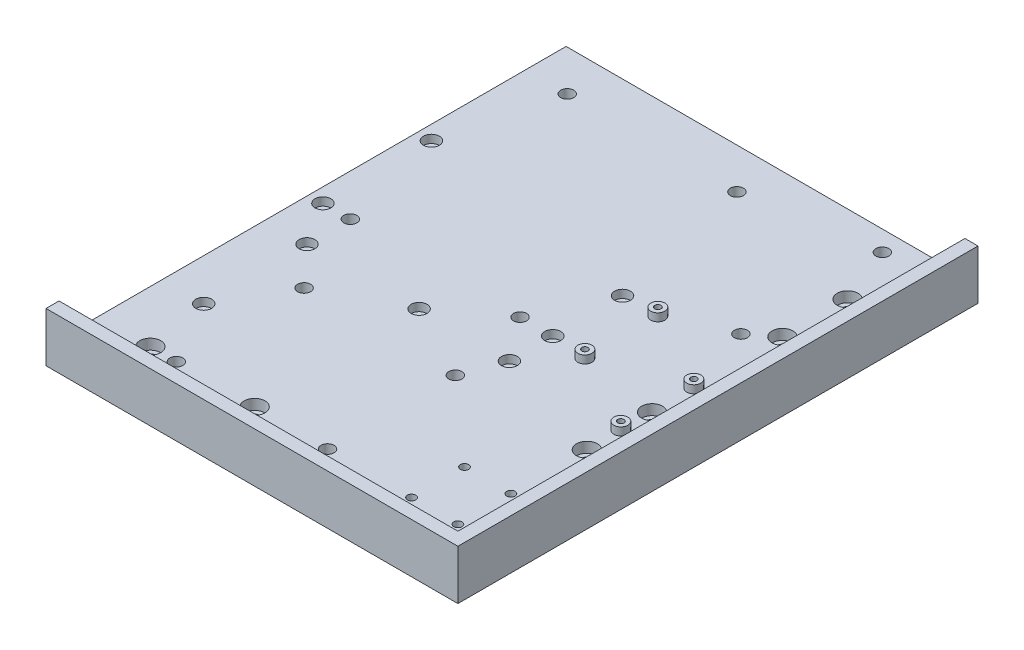
SolidWorks part; units mm, degrees
ref_plane "Front Plane" through (0, 0, 0) normal (0, 0, 1) x (1, 0, 0)
ref_plane "Top Plane" through (0, 0, 0) normal (0, 1, 0) x (1, 0, 0)
ref_plane "Right Plane" through (0, 0, 0) normal (1, 0, 0) x (0, 0, -1)
sketch "Sketch1" plane through (0, 0, 0) normal (0, 1, 0) x (1, 0, 0)
  line L1 (0, 0) -> (158, 0)
  line L2 (0, 0) -> (0, -199.5)
  line L3 (0, -199.5) -> (158, -199.5)
  line L4 (158, 0) -> (158, -199.5)
  dimension "D1" = 158
  dimension "D2" = 199.5
extrude "Boss-Extrude1" add sketch "Sketch1" along normal blind 6.35
sketch "Sketch2" [suppressed] plane through (0, 6.35, 0) normal (0, 1, 0) x (1, 0, 0)
  line L0 (0, -199.5) -> (158, -199.5) construction
  line L1 (158, -199.5) -> (77, -199.5)
  line L2 (158, -199.5) -> (158, -158.5)
  line L3 (158, -158.5) -> (77, -158.5)
  line L4 (77, -199.5) -> (77, -158.5)
  dimension "D1" = 81
  dimension "D2" = 41
sketch "Sketch3" plane through (0, 6.35, 0) normal (0, 1, 0) x (1, 0, 0)
  line L16 (158, -199.5) -> (158, 0) construction
  line L20 (0, -199.5) -> (158, -199.5) construction
  line L21 (158, -199.5) -> (158, 0)
  line L22 (0, -199.5) -> (158, -199.5)
  line L23 (0, -194.5) -> (153, -194.5)
  line L24 (153, -194.5) -> (153, 0)
  line L25 (158, 0) -> (153, 0)
  line L26 (0, -199.5) -> (0, -194.5)
  dimension "D1" = 5
extrude "Boss-Extrude2" add sketch "Sketch3" along normal blind 12.7
sketch "Sketch4" plane through (0, 6.35, 0) normal (0, -1, 0) x (1, 0, 0)
  line L0 (0, 179.5) -> (80, 179.5) construction
  line L1 (0, 0) -> (0, 199.5) construction
  line L3 (0, 199.5) -> (158, 199.5) construction
  line L4 (40, 179.5) -> (40, 188.5903) construction
  line L5 (138, 160) -> (138, 0) construction
  line L7 (158, 0) -> (0, 0) construction
  line L8 (158, 199.5) -> (158, 0) construction
  line L9 (138, 80) -> (152.6176, 80) construction
  point P8 (20, 179.5)
  point P11 (60, 179.5)
  point P20 (138, 130)
  point P21 (138, 105)
  point P22 (138, 30)
  point P23 (138, 80)
  point P24 (138, 55)
  dimension "D1" = 20
  dimension "D2" = 40
  dimension "D3" = 20
  dimension "D4" = 25
  dimension "D5" = 25
  dimension "D6" = 80
  dimension "D7" = 160
hole_wizard "CBORE for M4 SHCS1" positions "Sketch4" profile "Sketch5" counterbore size "M4" standard "ANSI Metric" end condition up to next
sketch "Sketch5" plane through (138, 6.35, 55) normal (1, 0, 0) x (0, 0, 1)
  line L0 (0, 0) -> (0, 6.35)
  line L1 (0, 6.35) -> (2.25, 6.35)
  line L3 (2.25, 6.35) -> (2.25, 4)
  line L4 (2.25, 4) -> (4, 4)
  line L5 (4, 4) -> (4, 0)
  line L7 (4, 0) -> (0, 0)
  line L11 (0, -6.35) -> (0, 107.95) construction
  dimension "Thru Hole Dia." = 4.5
  dimension "Thru Hole Depth" = 6.35
  dimension "C'Bore Dia." = 8
  dimension "C'Bore Depth" = 4
sketch "Sketch7" [suppressed] plane through (0, 0, 0) normal (0, 0, -1) x (-1, 0, 0)
  line L0 (-79, 19.05) -> (-79, 4.7647) construction
  line L1 (-158, 19.05) -> (0, 19.05) construction
  line L2 (-158, 19.05) -> (-158, 0) construction
  line L3 (-129, 19.05) -> (0, 19.05)
  line L4 (-129, 19.05) -> (-129, 9.05)
  line L5 (-129, 9.05) -> (0, 9.05)
  line L6 (0, 19.05) -> (0, 9.05)
  line L7 (0, 19.05) -> (0, 0) construction
  dimension "D2" = 10
  dimension "D3" = 29
extrude "Cut-Extrude2" [suppressed] cut sketch "Sketch7" against normal up to next
fillet "Fillet1" [suppressed] radius 5
fillet "Fillet2" [suppressed] radius 5
fillet "Fillet3" [suppressed] radius 5
sketch "Sketch8" plane through (0, 6.35, 0) normal (0, 1, 0) x (1, 0, 0)
  line L2 (153, 0) -> (153, -194.5) construction
  line L3 (153, 0) -> (0, 0) construction
  circle A0 centre (129.05, -62) radius 2.5
  circle A1 centre (129.05, -7.75) radius 2.5
  dimension "D1" = 5
  dimension "D2" = 54.25
  dimension "D3" = 23.95
  dimension "D4" = 7.75
extrude "eStop" cut sketch "Sketch8" against normal through all
sketch "Sketch9" plane through (0, 6.35, 0) normal (0, 1, 0) x (1, 0, 0)
  line L0 (153, 0) -> (0, 0) construction
  line L1 (81.1, -98.77) -> (16, -98.77) construction
  line L2 (81.1, -98.77) -> (81.1, -15.57) construction
  line L3 (81.1, -15.57) -> (16, -15.57) construction
  line L4 (16, -98.77) -> (16, -15.57) construction
  line L5 (81.1, -98.77) -> (16, -15.57) construction
  line L6 (81.1, -15.57) -> (16, -98.77) construction
  line L13 (0, 0) -> (0, -194.5) construction
  circle A0 centre (16, -15.57) radius 2.5
  circle A1 centre (81.1, -15.57) radius 2.5
  circle A2 centre (81.1, -98.77) radius 2.5
  circle A3 centre (16, -98.77) radius 2.5
  point P0 (48.55, -57.17)
  point P23 (138, -30)
  dimension "D5" = 5
  dimension "D7" = 16
  dimension "D1" = 83.2
  dimension "D2" = 65.1
  dimension "D6" = 57.17
extrude "NucleoAndPi" cut sketch "Sketch9" against normal through all
sketch "Sketch10" plane through (0, 6.35, 0) normal (0, 1, 0) x (1, 0, 0)
  line L1 (138, -72) -> (107.2, -72) construction
  line L2 (138, -72) -> (138, -89) construction
  line L3 (138, -89) -> (107.2, -89) construction
  line L4 (107.2, -72) -> (107.2, -89) construction
  line L5 (138, -72) -> (107.2, -89) construction
  line L6 (138, -89) -> (107.2, -72) construction
  circle A0 centre (138, -89) radius 1.2
  circle A1 centre (107.2, -72) radius 1.2
  circle A2 centre (138, -89) radius 2.7
  circle A3 centre (107.2, -72) radius 2.7
  circle A4 centre (129.05, -62) radius 2.5 construction
  point P0 (122.6, -80.5)
  point P18 (138, -55)
  dimension "D3" = 2.4
  dimension "D4" = 1.5
  dimension "D1" = 17
  dimension "D2" = 30.8
  dimension "D5" = 10
extrude "Bucks - Extrude" add sketch "Sketch10" along normal blind 3
sketch "Sketch11" plane through (0, 6.35, 0) normal (0, 1, 0) x (1, 0, 0)
  circle A0 centre (138, -89) radius 1.6
  circle A1 centre (107.2, -72) radius 1.6
  dimension "D1" = 3.2
extrude "Bucks - Cut" cut sketch "Sketch11" against normal up to next (6.35 mm away)
pattern_linear "Buck 2" count 2 spacing 28 along (0, 0, 1) of "Bucks - Extrude", "Bucks - Cut"
sketch "Sketch12" plane through (0, 6.35, 0) normal (0, 1, 0) x (1, 0, 0)
  line L1 (88, -179.5) -> (30, -179.5) construction
  line L2 (88, -179.5) -> (88, -130.5) construction
  line L3 (88, -130.5) -> (30, -130.5) construction
  line L4 (30, -179.5) -> (30, -130.5) construction
  circle A0 centre (30, -130.5) radius 2.5
  circle A1 centre (88, -130.5) radius 2.5
  circle A2 centre (88, -179.5) radius 2.5
  circle A3 centre (30, -179.5) radius 2.5
  point P4 (60, -179.5)
  point P12 (138, -130)
  dimension "D4" = 5
  dimension "D1" = 58
  dimension "D2" = 49
  dimension "D3" = 50
extrude "Pi" cut sketch "Sketch12" against normal through all
sketch "Sketch13" plane through (0, 6.35, 0) normal (0, 1, 0) x (1, 0, 0)
  line L1 (138, -159.18) -> (120.22, -159.18) construction
  line L2 (138, -159.18) -> (138, -179.5) construction
  line L3 (138, -179.5) -> (120.22, -179.5) construction
  line L4 (120.22, -159.18) -> (120.22, -179.5) construction
  circle A0 centre (120.22, -159.18) radius 1.6
  circle A1 centre (120.22, -179.5) radius 1.6
  circle A2 centre (138, -159.18) radius 1.6
  circle A3 centre (138, -179.5) radius 1.6
  point P8 (138, -130)
  point P9 (88, -179.5)
  dimension "D3" = 3.2
  dimension "D1" = 17.78
  dimension "D2" = 20.32
extrude "IMU" cut sketch "Sketch13" against normal through all
sketch "Sketch15" plane through (0, 6.35, 0) normal (0, 1, 0) x (1, 0, 0)
  line L0 (16, -15.57) -> (16, -98.77) construction
  line L1 (0, 0) -> (0, -194.5) construction
  line L3 (30, -130.5) -> (88, -130.5) construction
  line L4 (59, -115.385) -> (93.65, -115.385) construction
  line L5 (93.65, -98.77) -> (93.65, -115.385) construction
  line L6 (107.2, -72) -> (93.65, -72) construction
  line L7 (93.65, -98.77) -> (93.65, -72) construction
  line L8 (30, -130.5) -> (30, -179.5) construction
  circle A1 centre (5.5, -57.17) radius 3.05
  circle A2 centre (5.5, -98.77) radius 3.05
  circle A3 centre (16, -115.385) radius 3.05
  circle A4 centre (59, -115.385) radius 3.05
  circle A5 centre (93.65, -98.77) radius 3.05
  circle A6 centre (93.65, -115.385) radius 3.05
  circle A7 centre (93.65, -72) radius 3.05
  circle A8 centre (16, -155) radius 3.05
  point P1 (16, -57.17)
  point P21 (59, -130.5)
  point P24 (81.1, -98.77)
  point P36 (30, -155)
  dimension "D1" = 6.1
  dimension "D2" = 16.615
  dimension "D3" = 12.55
  dimension "D4" = 5.5
extrude "MAGNETS" cut sketch "Sketch15" against normal blind 3.1
ref_plane "Plane1" through (0, 0, 99.75) normal (0, 0, -1) x (-1, 0, 0)
sketch "Sketch16" plane through (0, 0, 194.5) normal (0, 0, -1) x (-1, 0, 0)
  line L4 (-153, 6.35) -> (0, 6.35)
  line L5 (0, 6.35) -> (0, 19.05)
  line L6 (0, 19.05) -> (-153, 19.05)
  line L7 (-153, 19.05) -> (-153, 6.35)
  line L8 (-153, 6.35) -> (0, 6.35)
  line L9 (0, 6.35) -> (0, 19.05)
  line L10 (0, 19.05) -> (-153, 19.05)
  line L11 (-153, 19.05) -> (-153, 6.35)
  dimension "D1" = 0
